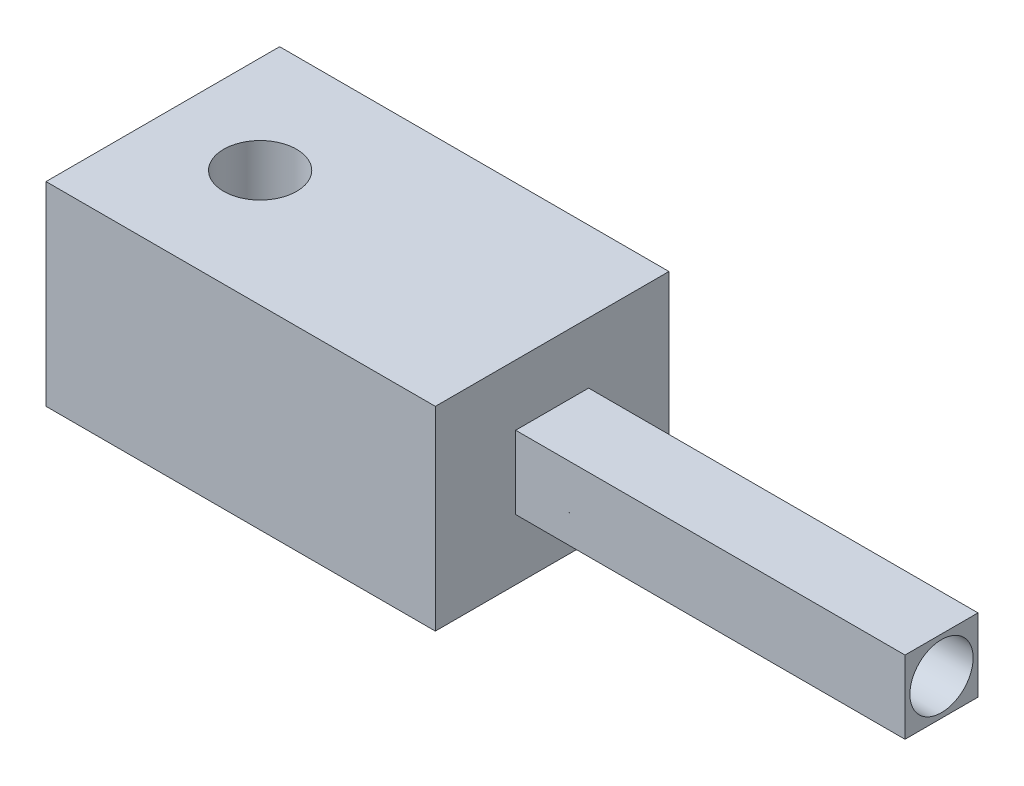
SolidWorks part; units mm, degrees
ref_plane "Front Plane" through (0, 0, 0) normal (0, 0, 1) x (1, 0, 0)
ref_plane "Top Plane" through (0, 0, 0) normal (0, 1, 0) x (1, 0, 0)
ref_plane "Right Plane" through (0, 0, 0) normal (1, 0, 0) x (0, 0, -1)
sketch "Sketch1" plane through (0, 0, 0) normal (1, 0, 0) x (0, 0, -1)
  line L1 (-3.75, 3.75) -> (3.75, 3.75)
  line L2 (-3.75, 3.75) -> (-3.75, -3.75)
  line L3 (-3.75, -3.75) -> (3.75, -3.75)
  line L4 (3.75, 3.75) -> (3.75, -3.75)
  line L5 (-3.75, 3.75) -> (3.75, -3.75) construction
  line L6 (-3.75, -3.75) -> (3.75, 3.75) construction
  point P0 (0, 0)
  dimension "D1" = 7.5
  dimension "D2" = 7.5
extrude "Boss-Extrude1" add sketch "Sketch1" along normal blind 40
sketch "Sketch2" plane through (0, 0, 0) normal (-1, 0, 0) x (0, 0, 1)
  line L1 (-12, 10) -> (12, 10)
  line L2 (-12, 10) -> (-12, -10)
  line L3 (-12, -10) -> (12, -10)
  line L4 (12, 10) -> (12, -10)
  line L5 (-12, 10) -> (12, -10) construction
  line L6 (-12, -10) -> (12, 10) construction
  point P0 (0, 0)
  dimension "D1" = 20
  dimension "D2" = 24
extrude "Boss-Extrude2" add sketch "Sketch2" along normal blind 40
sketch "Sketch3" plane through (40, 0, 0) normal (1, 0, 0) x (0, 0, -1)
  circle A0 centre (0, 0) radius 3.25
  dimension "D1" = 6.5
sketch "Sketch4" plane through (0, 10, 0) normal (0, 1, 0) x (1, 0, 0)
  line L0 (-40, -12) -> (-40, 12) construction
  circle A0 centre (-30, 0) radius 3.75
  point P4 (-30, 21.2989)
  point P5 (0, 0)
  dimension "D1" = 7.5
  dimension "D2" = 10
extrude "Cut-Extrude1" cut sketch "Sketch4" against normal up to surface (20 mm away) up to face at (-20, -10, 0)
extrude "Cut-Extrude2" cut sketch "Sketch3" against normal up to surface (40 mm away) up to face at (0, 0, 0)
